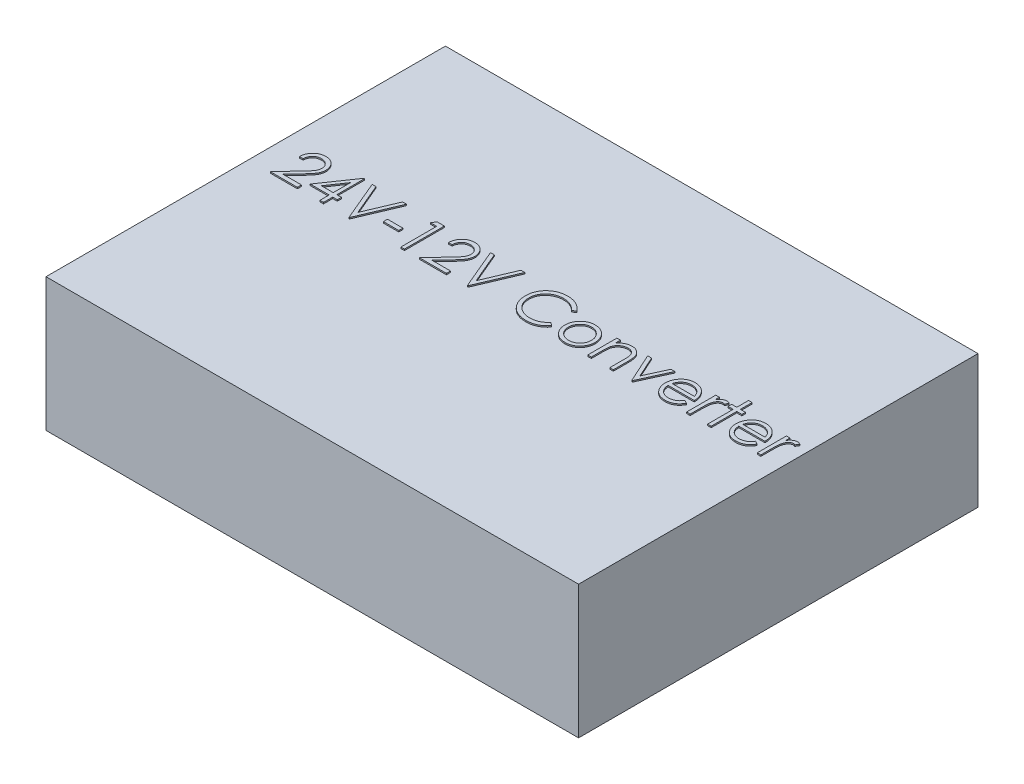
SolidWorks part; units mm, degrees
ref_plane "Front Plane" through (0, 0, 0) normal (0, 0, 1) x (1, 0, 0)
ref_plane "Top Plane" through (0, 0, 0) normal (0, 1, 0) x (1, 0, 0)
ref_plane "Right Plane" through (0, 0, 0) normal (1, 0, 0) x (0, 0, -1)
sketch "Sketch1" plane through (0, 0, 0) normal (0, 1, 0) x (1, 0, 0)
  line L1 (50.8, -38.1) -> (-50.8, -38.1)
  line L2 (50.8, -38.1) -> (50.8, 38.1)
  line L3 (50.8, 38.1) -> (-50.8, 38.1)
  line L4 (-50.8, -38.1) -> (-50.8, 38.1)
  line L5 (50.8, -38.1) -> (-50.8, 38.1) construction
  line L6 (50.8, 38.1) -> (-50.8, -38.1) construction
  point P0 (0, 0)
  dimension "D1" = 101.6
  dimension "D2" = 76.2
extrude "Boss-Extrude1" add sketch "Sketch1" along normal blind 25.4
sketch "Sketch2" plane through (0, 25.4, 0) normal (0, 1, 0) x (1, 0, 0)
  text T0 "24V-12V Converter" font "Century Gothic" height 7.62
extrude "Boss-Extrude2" add sketch "Sketch2" along normal blind 0.254
